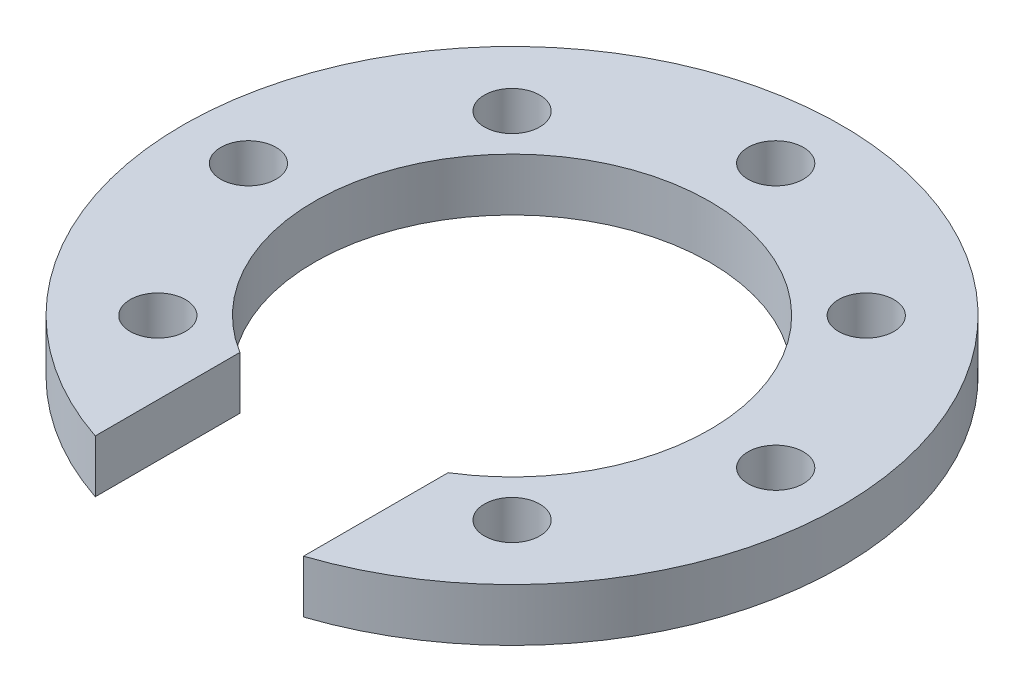
SolidWorks part; units mm, degrees
material "6061-T6 (SS)"
ref_plane "Front Plane" through (0, 0, 0) normal (0, 0, 1) x (1, 0, 0)
ref_plane "Top Plane" through (0, 0, 0) normal (0, 1, 0) x (1, 0, 0)
ref_plane "Right Plane" through (0, 0, 0) normal (1, 0, 0) x (0, 0, -1)
sketch "Sketch1" plane through (0, 0, 0) normal (0, 1, 0) x (1, 0, 0)
  circle A0 centre (0, 0) radius 7.5
  circle A1 centre (0, 0) radius 12.5
  dimension "D1" = 15
  dimension "D2" = 25
extrude "Boss-Extrude1" add sketch "Sketch1" along normal blind 2
sketch "Sketch2" plane through (0, 2, 0) normal (0, 1, 0) x (1, 0, 0)
  circle A0 centre (10, 0) radius 1.05
  dimension "D2" = 2.1
  dimension "D1" = 10
  dimension "D3" = 0
extrude "Cut-Extrude1" cut sketch "Sketch2" against normal blind 5
pattern_circular "CirPattern1" count 3 over 180 about axis through (0, 0, 0) along (0, 1, 0) of "Cut-Extrude1"
sketch "Sketch3" plane through (0, 2, 0) normal (0, 1, 0) x (1, 0, 0)
  circle A0 centre (-6.7175, 6.7175) radius 1.05
  circle A1 centre (6.7175, 6.7175) radius 1.05
  circle A2 centre (6.7175, -6.7175) radius 1.05
  circle A3 centre (-6.7175, -6.7175) radius 1.05
  dimension "D9" = 2.1
  dimension "D10" = 2.1
  dimension "D11" = 2.1
  dimension "D12" = 2.1
  dimension "D1" = 13.435
  dimension "D2" = 0
  dimension "D3" = 13.435
  dimension "D4" = 0
  dimension "D5" = 13.435
  dimension "D6" = 0
  dimension "D7" = 6.7175
  dimension "D8" = 6.7175
extrude "Cut-Extrude2" cut sketch "Sketch3" against normal blind 2
sketch "Sketch4" plane through (0, 2, 0) normal (0, 1, 0) x (1, 0, 0)
  line L0 (0, 0) -> (0, -10.2633)
  line L2 (-3.95, -15.9364) -> (3.95, -15.9364)
  line L3 (-3.95, -15.9364) -> (-3.95, -4.5901)
  line L4 (-3.95, -4.5901) -> (3.95, -4.5901)
  line L5 (3.95, -15.9364) -> (3.95, -4.5901)
  line L6 (-3.95, -15.9364) -> (3.95, -4.5901) construction
  line L7 (-3.95, -4.5901) -> (3.95, -15.9364) construction
  dimension "D1" = 7.9
extrude "Cut-Extrude3" cut sketch "Sketch4" against normal blind 10
